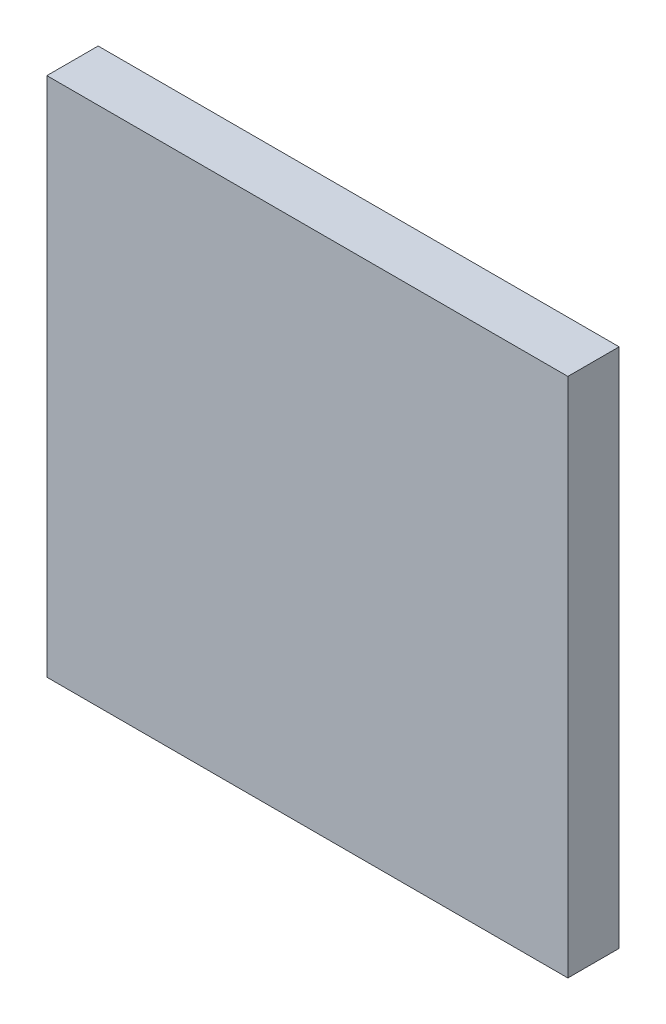
SolidWorks part; units mm, degrees
ref_plane "Front Plane" through (0, 0, 0) normal (0, 0, 1) x (1, 0, 0)
ref_plane "Top Plane" through (0, 0, 0) normal (0, 1, 0) x (1, 0, 0)
ref_plane "Right Plane" through (0, 0, 0) normal (1, 0, 0) x (0, 0, -1)
sketch "Sketch1" plane through (0, 0, 0) normal (0, 0, 1) x (1, 0, 0)
  line L1 (0, 0) -> (25.4, 0)
  line L2 (0, 0) -> (0, 25.4)
  line L3 (0, 25.4) -> (25.4, 25.4)
  line L4 (25.4, 0) -> (25.4, 25.4)
  dimension "D1" = 25.4
  dimension "D2" = 25.4
extrude "Boss-Extrude1" add sketch "Sketch1" along normal blind 2.5
